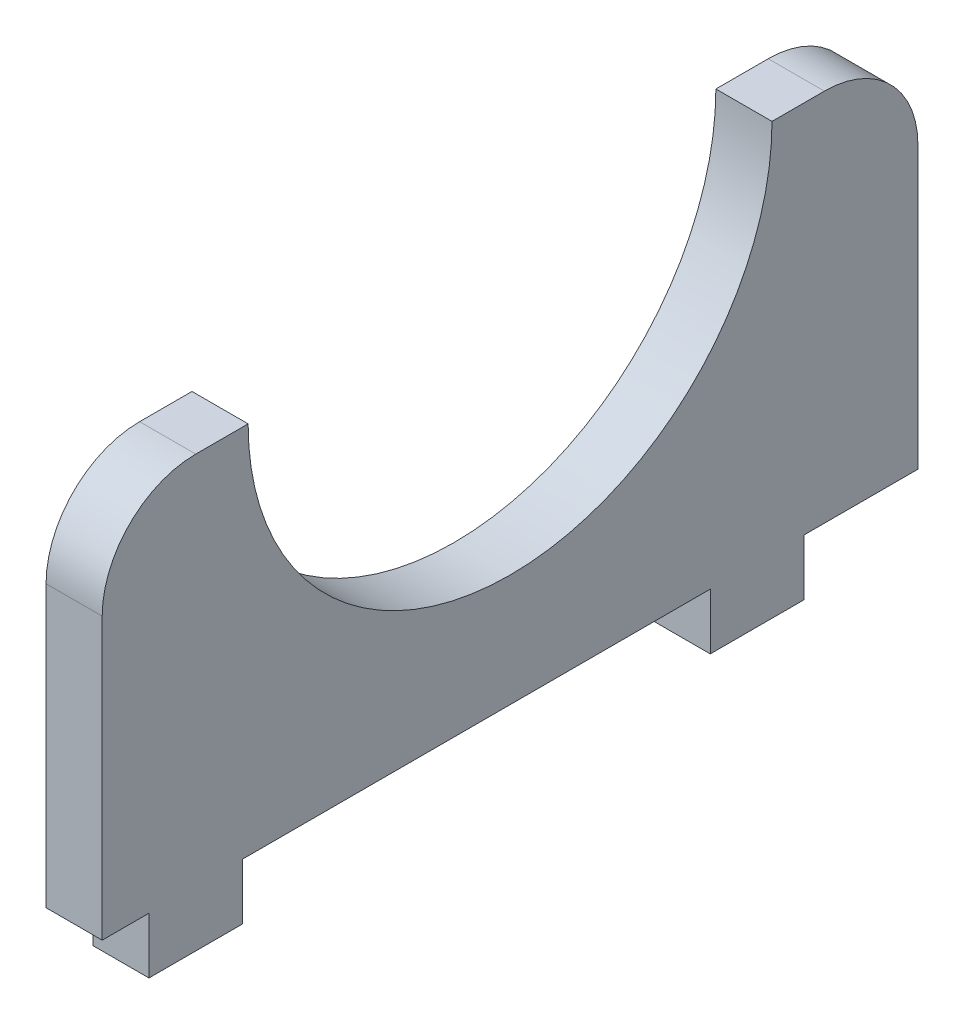
SolidWorks part; units mm, degrees
ref_plane "Front Plane" through (0, 0, 0) normal (0, 0, 1) x (1, 0, 0)
ref_plane "Top Plane" through (0, 0, 0) normal (0, 1, 0) x (1, 0, 0)
ref_plane "Right Plane" through (0, 0, 0) normal (1, 0, 0) x (0, 0, -1)
ref_plane "Plane1" through (0, -2, 0) normal (0, 1, 0) x (1, 0, 0)
sketch "Sketch1" plane through (0, 0, 0) normal (1, 0, 0) x (0, 0, -1)
  line L1 (13.6, -11.75) -> (-30, -11.75)
  line L2 (13.6, -11.75) -> (13.6, 8.25)
  line L3 (13.6, 8.25) -> (-30, 8.25)
  line L4 (-30, -11.75) -> (-30, 8.25)
  point P0 (0, 0)
  dimension "D1" = 20
  dimension "D2" = 43.6
extrude "Boss-Extrude1" add sketch "Sketch1" along normal blind 3
sketch "Sketch4" plane through (3, 0, 0) normal (1, 0, 0) x (0, 0, -1)
  line L0 (13.6, 8.25) -> (-30, 8.25) construction
  line L1 (13.6, -11.75) -> (13.6, 8.25) construction
  circle A0 centre (-8.2, 8.25) radius 14
  dimension "D1" = 28
  dimension "D2" = 21.8
extrude "Cut-Extrude1" cut sketch "Sketch4" against normal through all
fillet "Fillet1" radius 5 2 edges at (1.5, 8.25, -13.6) (1.5, 8.25, 30)
sketch "Sketch3" plane through (0, -11.75, 0) normal (0, -1, 0) x (1, 0, 0)
  line L0 (3, 30) -> (3, -13.6) construction
  line L1 (3, 27.5) -> (0, 27.5)
  line L2 (3, 27.5) -> (3, 22.5)
  line L3 (3, 22.5) -> (0, 22.5)
  line L4 (0, 27.5) -> (0, 22.5)
  line L5 (0, 30) -> (0, -13.6) construction
  line L6 (3, 30) -> (0, 30) construction
  dimension "D1" = 2.5
  dimension "D2" = 5
extrude "Boss-Extrude2" add sketch "Sketch3" along normal blind 3
pattern_linear "LPattern1" count 2 spacing 30 along (0, 0, -1) of "Boss-Extrude2"
